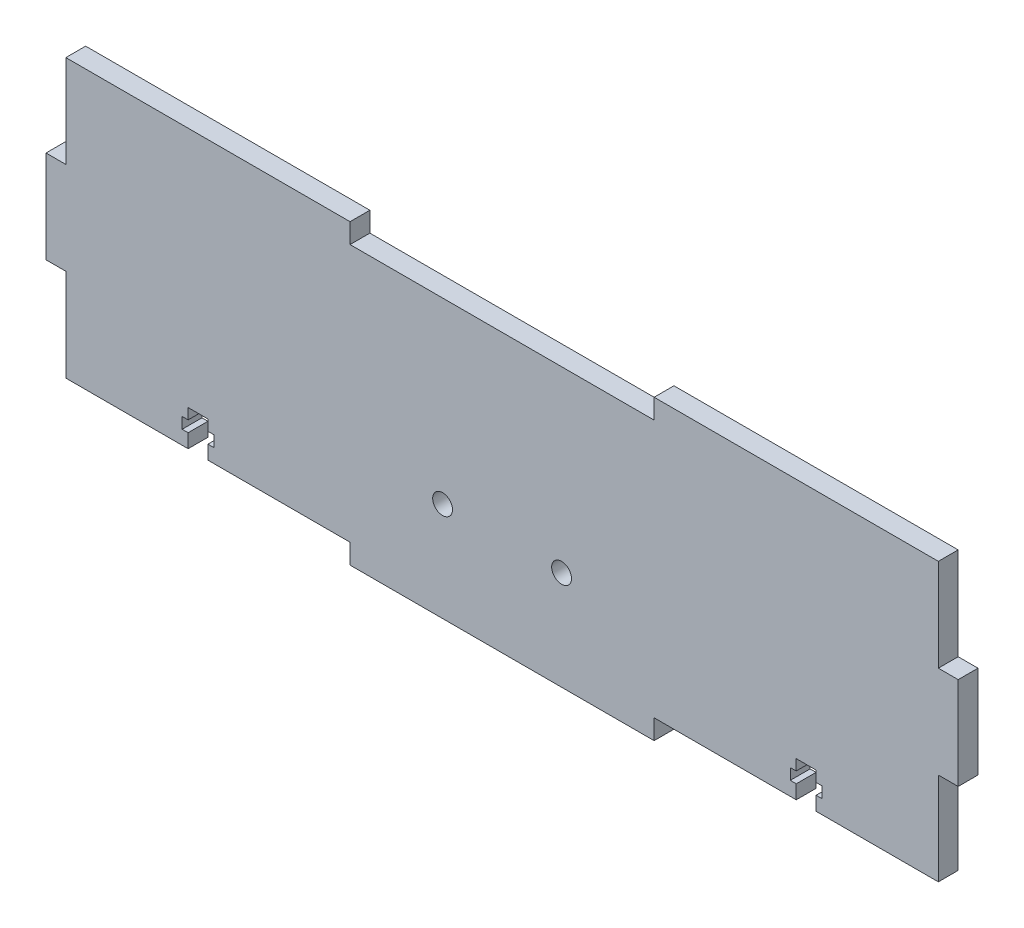
SolidWorks part; units mm, degrees
ref_plane "Alzado" through (0, 0, 0) normal (0, 0, 1) x (1, 0, 0)
ref_plane "Planta" through (0, 0, 0) normal (0, 1, 0) x (1, 0, 0)
ref_plane "Vista lateral" through (0, 0, 0) normal (1, 0, 0) x (0, 0, -1)
sketch "Croquis1" plane through (0, 0, 0) normal (0, 0, 1) x (1, 0, 0)
  line L0 (115, 0) -> (115, 23.3303) construction
  line L1 (0, 0) -> (230, 0)
  line L2 (0, 0) -> (0, 75)
  line L3 (0, 75) -> (230, 75)
  line L4 (230, 0) -> (230, 75)
  line L5 (0, 75) -> (5, 75)
  line L6 (0, 75) -> (0, 0)
  line L7 (0, 0) -> (5, 0)
  line L8 (5, 75) -> (5, 0)
  line L9 (225, 75) -> (225, 0)
  line L10 (76.6667, 5) -> (76.6667, 0)
  line L11 (0, 0) -> (230, 0)
  line L12 (0, 0) -> (0, 5)
  line L13 (0, 5) -> (230, 5)
  line L14 (230, 0) -> (230, 5)
  line L15 (153.3333, 0) -> (153.3333, 5)
  line L16 (0, 51.6667) -> (5, 51.6667)
  line L17 (5, 28.3333) -> (0, 28.3333)
  line L18 (225, 28.3333) -> (230, 28.3333)
  line L19 (230, 51.6667) -> (225, 51.6667)
  point P21 (2.5, 51.6667)
  dimension "D1" = 230
  dimension "D2" = 75
  dimension "D3" = 5
  dimension "D4" = 5
  dimension "D5" = 76.6667
  dimension "D6" = 76.6667
  dimension "D7" = 23.3333
  dimension "D8" = 23.3333
extrude "Saliente-Extruir1" add sketch "Croquis1" along normal blind 5
sketch "Croquis2" plane through (0, 0, 5) normal (0, 0, 1) x (1, 0, 0)
  line L0 (38.3333, 5) -> (38.3333, 14) construction
  line L1 (5, 5) -> (76.6667, 5) construction
  line L2 (115, 0) -> (115, 11.3726) construction
  line L3 (76.6667, 0) -> (153.3333, 0) construction
  line L4 (35.8333, 5) -> (35.8333, 8.5)
  line L5 (35.8333, 8.5) -> (34.3333, 8.5)
  line L6 (34.3333, 8.5) -> (34.3333, 11.3)
  line L7 (34.3333, 11.3) -> (35.8333, 11.3)
  line L8 (35.8333, 11.3) -> (35.8333, 14)
  line L9 (35.8333, 14) -> (40.8333, 14)
  line L10 (40.8333, 11.3) -> (40.8333, 14)
  line L11 (42.3333, 11.3) -> (40.8333, 11.3)
  line L12 (42.3333, 8.5) -> (42.3333, 11.3)
  line L13 (40.8333, 8.5) -> (42.3333, 8.5)
  line L14 (40.8333, 5) -> (40.8333, 8.5)
  line L15 (191.6667, 5) -> (191.6667, 14) construction
  line L16 (189.1667, 5) -> (189.1667, 8.5)
  line L17 (189.1667, 8.5) -> (187.6667, 8.5)
  line L18 (187.6667, 8.5) -> (187.6667, 11.3)
  line L19 (187.6667, 11.3) -> (189.1667, 11.3)
  line L20 (189.1667, 11.3) -> (189.1667, 14)
  line L21 (194.1667, 14) -> (189.1667, 14)
  line L22 (194.1667, 11.3) -> (194.1667, 14)
  line L23 (195.6667, 11.3) -> (194.1667, 11.3)
  line L24 (195.6667, 8.5) -> (195.6667, 11.3)
  line L25 (194.1667, 8.5) -> (195.6667, 8.5)
  line L26 (194.1667, 5) -> (194.1667, 8.5)
  line L27 (40.8333, 5) -> (35.8333, 5)
  line L28 (194.1667, 5) -> (189.1667, 5)
  line L29 (0, 28.3333) -> (0, 51.6667) construction
  point P10 (35.0833, 11.3)
  point P38 (38.3333, 9.5)
  dimension "D1" = 2.8
  dimension "D2" = 4
  dimension "D3" = 9
  dimension "D4" = 3.5
  dimension "D5" = 2.5
  dimension "D6" = 38.3333
extrude "Cortar-Extruir1" cut sketch "Croquis2" against normal blind 5
sketch "Croquis3" plane through (0, 0, 5) normal (0, 0, 1) x (1, 0, 0)
  line L0 (5, 75) -> (225, 75) construction
  line L1 (76.6667, 75) -> (153.3333, 75)
  line L2 (76.6667, 75) -> (76.6667, 70)
  line L3 (76.6667, 70) -> (153.3333, 70)
  line L4 (153.3333, 75) -> (153.3333, 70)
  line L5 (0, 28.3333) -> (0, 51.6667) construction
  line L6 (230, 28.3333) -> (230, 51.6667) construction
  dimension "D1" = 5
  dimension "D2" = 76.6667
  dimension "D3" = 76.6667
extrude "Cortar-Extruir2" cut sketch "Croquis3" against normal blind 10
sketch "Croquis4" plane through (0, 0, 5) normal (0, 0, 1) x (1, 0, 0)
  line L0 (115, 0) -> (115, 25) construction
  line L1 (76.6667, 0) -> (153.3333, 0) construction
  line L2 (100, 25) -> (115, 25) construction
  line L3 (40.8333, 5) -> (76.6667, 5) construction
  circle A0 centre (100, 25) radius 2.5
  circle A1 centre (130, 25) radius 2.5
  dimension "D1" = 5
  dimension "D2" = 15
  dimension "D3" = 20
extrude "Cortar-Extruir3" cut sketch "Croquis4" against normal blind 10
sketch "Croquis5" plane through (0, 0, 5) normal (0, 0, 1) x (1, 0, 0)
  line L44 (76.6667, 70) -> (76.6667, 75)
  line L45 (76.6667, 75) -> (5, 75)
  line L46 (5, 75) -> (5, 51.6667)
  line L47 (5, 51.6667) -> (0, 51.6667)
  line L48 (0, 51.6667) -> (0, 28.3333)
  line L49 (0, 28.3333) -> (5, 28.3333)
  line L50 (5, 28.3333) -> (5, 5)
  line L51 (5, 5) -> (35.8333, 5)
  line L52 (35.8333, 5) -> (35.8333, 8.5)
  line L53 (35.8333, 8.5) -> (34.3333, 8.5)
  line L54 (34.3333, 8.5) -> (34.3333, 11.3)
  line L55 (34.3333, 11.3) -> (35.8333, 11.3)
  line L56 (35.8333, 11.3) -> (35.8333, 14)
  line L57 (35.8333, 14) -> (40.8333, 14)
  line L58 (40.8333, 14) -> (40.8333, 11.3)
  line L59 (40.8333, 11.3) -> (42.3333, 11.3)
  line L60 (42.3333, 11.3) -> (42.3333, 8.5)
  line L61 (42.3333, 8.5) -> (40.8333, 8.5)
  line L62 (40.8333, 8.5) -> (40.8333, 5)
  line L63 (40.8333, 5) -> (76.6667, 5)
  line L64 (76.6667, 5) -> (76.6667, 0)
  line L65 (76.6667, 0) -> (153.3333, 0)
  line L66 (153.3333, 0) -> (153.3333, 5)
  line L67 (153.3333, 5) -> (189.1667, 5)
  line L68 (189.1667, 5) -> (189.1667, 8.5)
  line L69 (189.1667, 8.5) -> (187.6667, 8.5)
  line L70 (187.6667, 8.5) -> (187.6667, 11.3)
  line L71 (187.6667, 11.3) -> (189.1667, 11.3)
  line L72 (189.1667, 11.3) -> (189.1667, 14)
  line L73 (189.1667, 14) -> (194.1667, 14)
  line L74 (194.1667, 14) -> (194.1667, 11.3)
  line L75 (194.1667, 11.3) -> (195.6667, 11.3)
  line L76 (195.6667, 11.3) -> (195.6667, 8.5)
  line L77 (195.6667, 8.5) -> (194.1667, 8.5)
  line L78 (194.1667, 8.5) -> (194.1667, 5)
  line L79 (194.1667, 5) -> (225, 5)
  line L80 (225, 5) -> (225, 28.3333)
  line L81 (225, 28.3333) -> (230, 28.3333)
  line L82 (230, 28.3333) -> (230, 51.6667)
  line L83 (230, 51.6667) -> (225, 51.6667)
  line L84 (225, 51.6667) -> (225, 75)
  line L85 (225, 75) -> (153.3333, 75)
  line L86 (153.3333, 75) -> (153.3333, 70)
  line L87 (153.3333, 70) -> (76.6667, 70)
  line L88 (76.6667, 70) -> (76.6667, 75)
  line L89 (76.6667, 75) -> (5, 75)
  line L90 (5, 75) -> (5, 51.6667)
  line L91 (5, 51.6667) -> (0, 51.6667)
  line L92 (0, 51.6667) -> (0, 28.3333)
  line L93 (0, 28.3333) -> (5, 28.3333)
  line L94 (5, 28.3333) -> (5, 5)
  line L95 (5, 5) -> (35.8333, 5)
  line L96 (35.8333, 5) -> (35.8333, 8.5)
  line L97 (35.8333, 8.5) -> (34.3333, 8.5)
  line L98 (34.3333, 8.5) -> (34.3333, 11.3)
  line L99 (34.3333, 11.3) -> (35.8333, 11.3)
  line L100 (35.8333, 11.3) -> (35.8333, 14)
  line L101 (35.8333, 14) -> (40.8333, 14)
  line L102 (40.8333, 14) -> (40.8333, 11.3)
  line L103 (40.8333, 11.3) -> (42.3333, 11.3)
  line L104 (42.3333, 11.3) -> (42.3333, 8.5)
  line L105 (42.3333, 8.5) -> (40.8333, 8.5)
  line L106 (40.8333, 8.5) -> (40.8333, 5)
  line L107 (40.8333, 5) -> (76.6667, 5)
  line L108 (76.6667, 5) -> (76.6667, 0)
  line L109 (76.6667, 0) -> (153.3333, 0)
  line L110 (153.3333, 0) -> (153.3333, 5)
  line L111 (153.3333, 5) -> (189.1667, 5)
  line L112 (189.1667, 5) -> (189.1667, 8.5)
  line L113 (189.1667, 8.5) -> (187.6667, 8.5)
  line L114 (187.6667, 8.5) -> (187.6667, 11.3)
  line L115 (187.6667, 11.3) -> (189.1667, 11.3)
  line L116 (189.1667, 11.3) -> (189.1667, 14)
  line L117 (189.1667, 14) -> (194.1667, 14)
  line L118 (194.1667, 14) -> (194.1667, 11.3)
  line L119 (194.1667, 11.3) -> (195.6667, 11.3)
  line L120 (195.6667, 11.3) -> (195.6667, 8.5)
  line L121 (195.6667, 8.5) -> (194.1667, 8.5)
  line L122 (194.1667, 8.5) -> (194.1667, 5)
  line L123 (194.1667, 5) -> (225, 5)
  line L124 (225, 5) -> (225, 28.3333)
  line L125 (225, 28.3333) -> (230, 28.3333)
  line L126 (230, 28.3333) -> (230, 51.6667)
  line L127 (230, 51.6667) -> (225, 51.6667)
  line L128 (225, 51.6667) -> (225, 75)
  line L129 (225, 75) -> (153.3333, 75)
  line L130 (153.3333, 75) -> (153.3333, 70)
  line L131 (153.3333, 70) -> (76.6667, 70)
  circle A0 centre (130, 25) radius 2.5 construction
  circle A1 centre (100, 25) radius 2.5 construction
  circle A2 centre (130, 25) radius 2.5
  circle A3 centre (100, 25) radius 2.5
  dimension "D1" = 0
